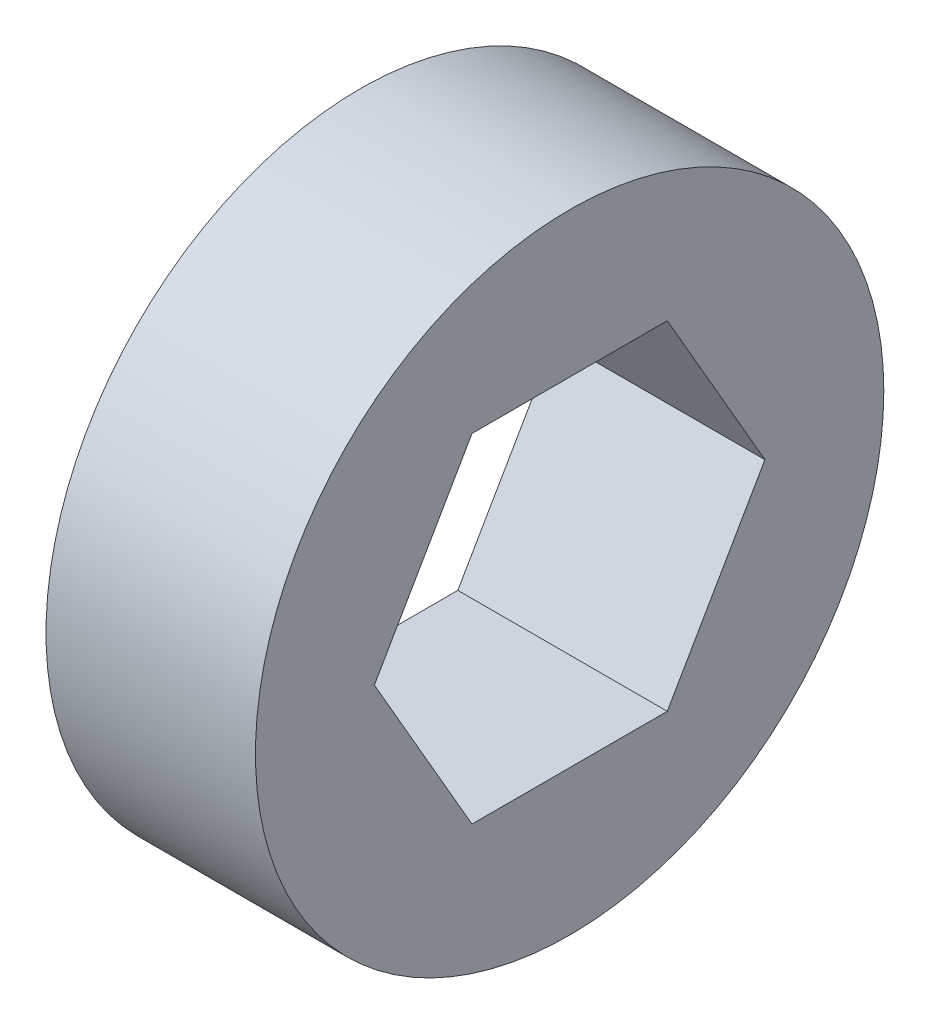
SolidWorks part; units mm, degrees
material "PET"
ref_plane "Front" through (0, 0, 0) normal (0, 0, 1) x (1, 0, 0)
ref_plane "Top" through (0, 0, 0) normal (0, 1, 0) x (1, 0, 0)
ref_plane "Right" through (0, 0, 0) normal (1, 0, 0) x (0, 0, -1)
sketch "Sketch1" plane through (0, 0, 0) normal (1, 0, 0) x (0, 0, -1)
  line L1 (1.48, 2.5635) -> (-1.48, 2.5635)
  line L2 (-1.48, 2.5635) -> (-2.9601, 0)
  line L3 (-2.9601, 0) -> (-1.48, -2.5635)
  line L4 (-1.48, -2.5635) -> (1.48, -2.5635)
  line L5 (1.48, -2.5635) -> (2.9601, 0)
  line L6 (2.9601, 0) -> (1.48, 2.5635)
  circle A0 centre (0, 0) radius 4.7625
  circle A1 centre (0, 0) radius 2.5635 construction
  dimension "D2" = 9.525
  dimension "D1" = 5.127
extrude "Boss-Extrude1" add sketch "Sketch1" along normal blind 3.175
